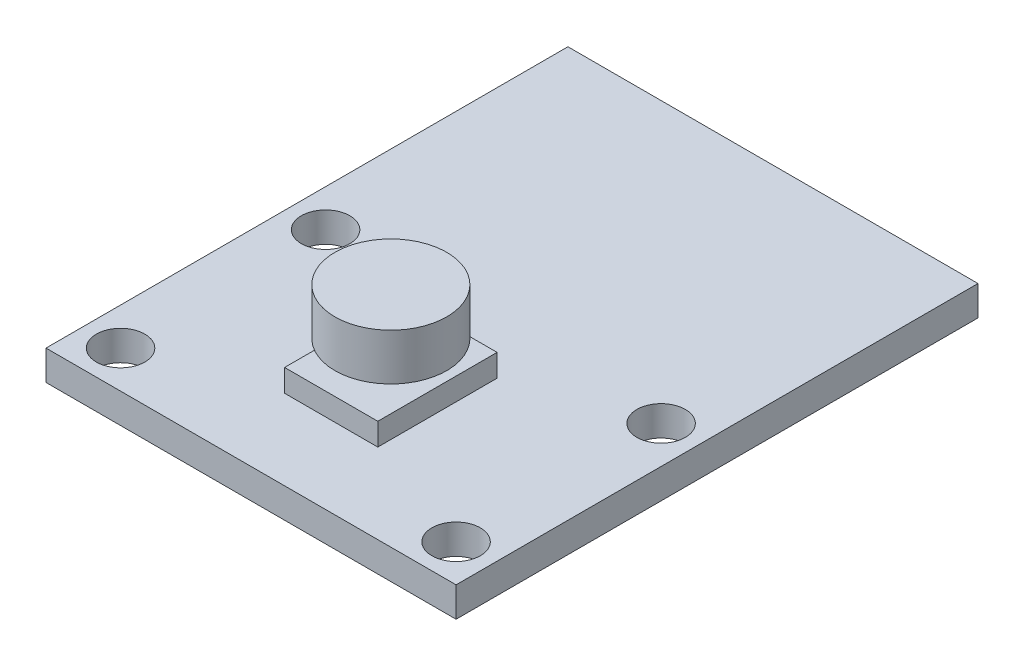
SolidWorks part; units mm, degrees
ref_plane "Plan de face" through (0, 0, 0) normal (0, 0, 1) x (1, 0, 0)
ref_plane "Plan de dessus" through (0, 0, 0) normal (0, 1, 0) x (1, 0, 0)
ref_plane "Plan de droite" through (0, 0, 0) normal (1, 0, 0) x (0, 0, -1)
sketch "Esquisse1" plane through (0, 0, 0) normal (0, 1, 0) x (1, 0, 0)
  line L0 (0, -7.5) -> (0, 20.5) construction
  line L1 (-11, 20.5) -> (11, 20.5)
  line L2 (-11, 20.5) -> (-11, -7.5)
  line L3 (-11, -7.5) -> (11, -7.5)
  line L4 (11, 20.5) -> (11, -7.5)
  line L5 (-7.7297, 0) -> (8.3243, 0) construction
  circle A0 centre (-9, 5.5) radius 1.3
  circle A1 centre (9, 5.5) radius 1.3
  circle A2 centre (9, -5.5) radius 1.3
  circle A3 centre (-9, -5.5) radius 1.3
  dimension "D6" = 2.6
  dimension "D1" = 11
  dimension "D2" = 28
  dimension "D3" = 22
  dimension "D4" = 18
  dimension "D5" = 7.5
extrude "Boss.-Extru.1" add sketch "Esquisse1" along normal blind 1.6
sketch "Esquisse2" plane through (0, 1.6, 0) normal (0, 1, 0) x (1, 0, 0)
  line L0 (-2.5, 3.2) -> (2.5, -3.2) construction
  line L1 (-2.5, 3.2) -> (2.5, 3.2)
  line L2 (-2.5, 3.2) -> (-2.5, -3.2)
  line L3 (-2.5, -3.2) -> (2.5, -3.2)
  line L4 (2.5, 3.2) -> (2.5, -3.2)
  dimension "D1" = 6.4
  dimension "D2" = 5
extrude "Boss.-Extru.2" add sketch "Esquisse2" along normal blind 1.2
sketch "Esquisse3" plane through (0, 2.8, 0) normal (0, 1, 0) x (1, 0, 0)
  circle A0 centre (0, 0) radius 3
  dimension "D1" = 6
extrude "Boss.-Extru.3" add sketch "Esquisse3" along normal blind 2.5 from offset 1 separate body
